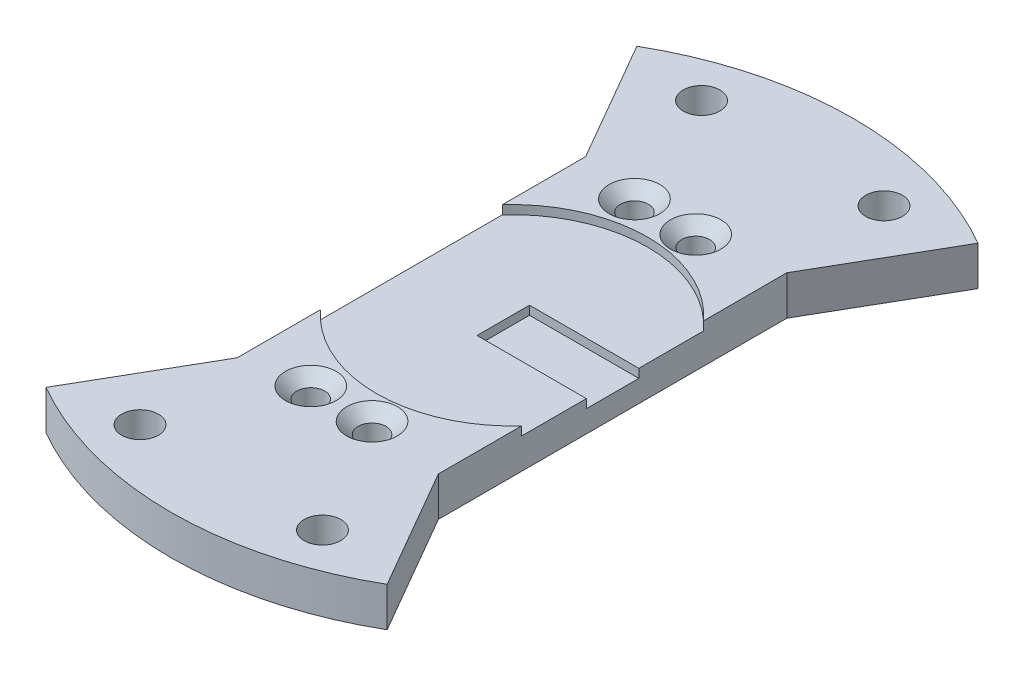
SolidWorks part; units mm, degrees
ref_plane "Front Plane" through (0, 0, 0) normal (0, 0, 1) x (1, 0, 0)
ref_plane "Top Plane" through (0, 0, 0) normal (0, 1, 0) x (1, 0, 0)
ref_plane "Right Plane" through (0, 0, 0) normal (1, 0, 0) x (0, 0, -1)
sketch "Sketch1" plane through (0, 0, 0) normal (0, 1, 0) x (1, 0, 0)
  line L0 (-33.75, 0) -> (0, 0) construction
  line L1 (0, 0) -> (-19.5, 33.775)
  line L2 (0, 0) -> (19.5, 33.775)
  line L3 (0, 0) -> (0, 39) construction
  line L4 (0, 0) -> (-19.5, -33.775)
  line L5 (0, 0) -> (19.5, -33.775)
  line L6 (-11.5, 19.9186) -> (-11.5, -19.9186)
  line L7 (11.5, 19.9186) -> (11.5, -19.9186)
  circle A0 centre (0, 0) radius 39
  circle A1 centre (-33.75, 0) radius 2.1
  circle A2 centre (-27.3043, 19.8378) radius 2.1
  circle A3 centre (-10.4293, 32.0982) radius 2.1
  circle A4 centre (10.4293, 32.0982) radius 2.1
  circle A5 centre (27.3043, 19.8378) radius 2.1
  circle A6 centre (33.75, 0) radius 2.1
  circle A7 centre (27.3043, -19.8378) radius 2.1
  circle A8 centre (10.4293, -32.0982) radius 2.1
  circle A9 centre (-10.4293, -32.0982) radius 2.1
  circle A10 centre (-27.3043, -19.8378) radius 2.1
  dimension "D1" = 78
  dimension "D3" = 4.2
  dimension "D2" = 33.75
  dimension "D5" = 30
  dimension "D6" = 30
  dimension "D7" = 30
  dimension "D8" = 30
  dimension "D9" = 23
  dimension "D10" = 11.5
  dimension "D4" = 10
extrude "Boss-Extrude1" add sketch "Sketch1" along normal blind 4.5 contours L4 A0 L5 A9 A8 | L7 L2 L5 | L2 A0 L1 A4 A3 | L1 L6 L4
sketch "Sketch2" plane through (0, 4.5, 0) normal (0, 1, 0) x (1, 0, 0)
  circle A0 centre (0, 0) radius 15.5
  dimension "D1" = 31
extrude "Cut-Extrude1" cut sketch "Sketch2" against normal blind 1
sketch "Sketch3" plane through (0, 3.5, 0) normal (0, 1, 0) x (1, 0, 0)
  line L0 (11.5, 10.3923) -> (11.5, -10.3923) construction
  line L1 (11.5, 3) -> (-1, 3)
  line L2 (11.5, 3) -> (11.5, -3)
  line L3 (11.5, -3) -> (-1, -3)
  line L4 (-1, 3) -> (-1, -3)
  dimension "D1" = 12.5
  dimension "D2" = 6
  dimension "D3" = 3
extrude "Cut-Extrude2" cut sketch "Sketch3" against normal blind 1
sketch "Sketch4" plane through (0, 4.5, 0) normal (0, 1, 0) x (1, 0, 0)
  line L0 (-11.5, 19.9186) -> (-11.5, 10.3923) construction
  circle A0 centre (-4.5, -18.5) radius 1.6
  circle A1 centre (2.5, -18.5) radius 1.6
  circle A2 centre (-4.5, 18.5) radius 1.6
  circle A3 centre (2.5, 18.5) radius 1.6
  dimension "D1" = 3.2
  dimension "D2" = 3.2
  dimension "D3" = 3.2
  dimension "D4" = 3.2
  dimension "D5" = 7
  dimension "D6" = 7
  dimension "D7" = 37
  dimension "D8" = 18.5
extrude "Cut-Extrude3" cut sketch "Sketch4" against normal through all
hole_wizard "CSK for M4 Countersunk Flat Head Screw1" positions "3DSketch1" profile "Sketch5" countersink size "M4" standard "ISO" end condition through all
sketch3d "3DSketch1"
  line L0 (-4.5, 0, 18.5) -> (-4.5, 4.5, 18.5) construction
  line L1 (2.5, 0, 18.5) -> (2.5, 4.5, 18.5) construction
  line L2 (-4.5, 0, -18.5) -> (-4.5, 4.5, -18.5) construction
  line L3 (2.5, 0, -18.5) -> (2.5, 4.5, -18.5) construction
  point P0 (-4.5, 4.5, 18.5)
  point P4 (2.5, 4.5, 18.5)
  point P8 (-4.5, 4.5, -18.5)
  point P12 (2.5, 4.5, -18.5)
sketch "Sketch5" plane through (-4.5, 4.5, 18.5) normal (1, 0, 0) x (0, 0, 1)
  line L0 (0, 0) -> (0, 4.5)
  line L1 (0, 4.5) -> (1.6, 4.5)
  line L2 (1.6, 4.5) -> (1.6, 1.3)
  line L3 (1.6, 1.3) -> (2.9, 0)
  line L5 (2.9, 0) -> (0, 0)
  line L6 (-1.6, 1.3) -> (-2.9, 0) construction
  line L11 (0, -6.35) -> (0, 107.95) construction
  dimension "Thru Hole Dia." = 3.2
  dimension "Thru Hole Depth" = 4.5
  dimension "Near C'Sink Dia." = 5.8
  dimension "Near C'Sink Angle" = 90
